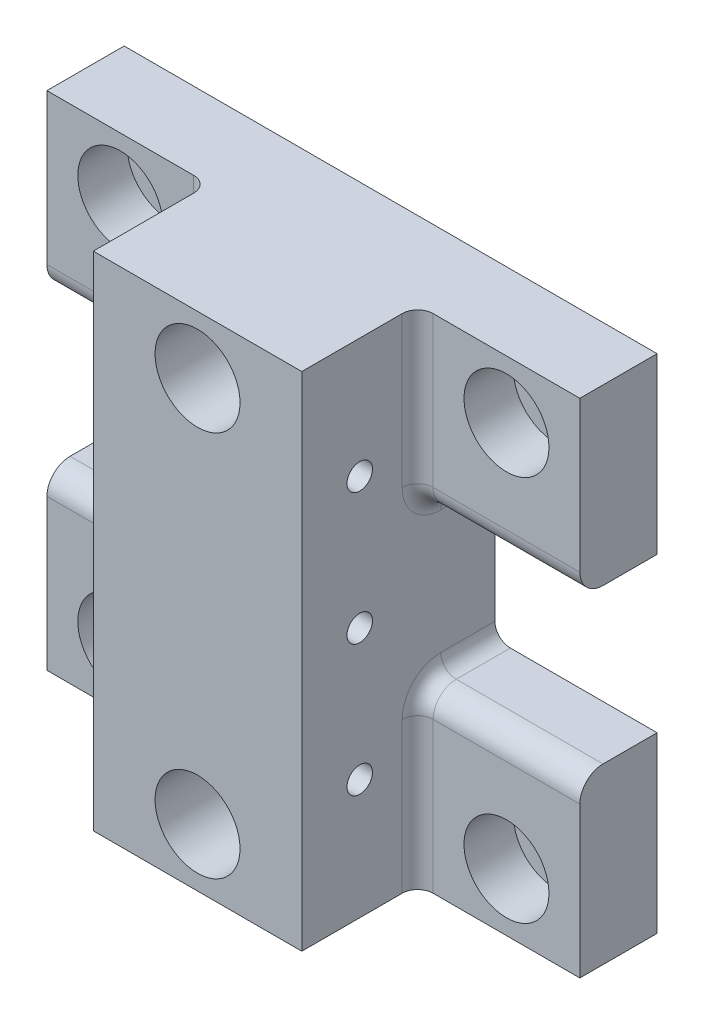
SolidWorks part; units mm, degrees
ref_plane "정면" through (0, 0, 0) normal (0, 0, 1) x (1, 0, 0)
ref_plane "윗면" through (0, 0, 0) normal (0, 1, 0) x (1, 0, 0)
ref_plane "우측면" through (0, 0, 0) normal (1, 0, 0) x (0, 0, -1)
sketch "스케치1" plane through (0, 0, 0) normal (0, 0, 1) x (1, 0, 0)
  line L1 (-34.5, -32.5) -> (34.5, -32.5)
  line L2 (-34.5, -32.5) -> (-34.5, 32.5)
  line L3 (-34.5, 32.5) -> (34.5, 32.5)
  line L4 (34.5, -32.5) -> (34.5, 32.5)
  line L5 (-34.5, -32.5) -> (34.5, 32.5) construction
  line L6 (-34.5, 32.5) -> (34.5, -32.5) construction
  point P0 (0, 0)
  dimension "D1" = 69
  dimension "D2" = 65
extrude "보스-돌출1" add sketch "스케치1" along normal blind 10
sketch "스케치2" plane through (0, 0, 10) normal (0, 0, 1) x (1, 0, 0)
  line L0 (34.5, 32.5) -> (-34.5, 32.5) construction
  line L1 (-13.5, -32.5) -> (13.5, -32.5)
  line L2 (-13.5, -32.5) -> (-13.5, 32.5)
  line L3 (-13.5, 32.5) -> (13.5, 32.5)
  line L4 (13.5, -32.5) -> (13.5, 32.5)
  line L5 (-13.5, -32.5) -> (13.5, 32.5) construction
  line L6 (-13.5, 32.5) -> (13.5, -32.5) construction
  point P0 (0, 0)
  dimension "D1" = 27
extrude "보스-돌출2" add sketch "스케치2" along normal blind 15
sketch "스케치3" plane through (13.5, 0, 0) normal (1, 0, 0) x (0, 0, -1)
  line L0 (0, -32.5) -> (0, 32.5) construction
  line L1 (-10, -10) -> (0, -10)
  line L2 (-10, -10) -> (-10, 10)
  line L3 (-10, 10) -> (0, 10)
  line L4 (0, -10) -> (0, 10)
  line L5 (-10, -10) -> (0, 10) construction
  line L6 (-10, 10) -> (0, -10) construction
  line L7 (-10, -32.5) -> (-10, 32.5) construction
  point P0 (-5, 0)
  dimension "D1" = 20
extrude "컷-돌출1" cut sketch "스케치3" along normal through all
mirror "대칭 복사1" about plane through (0, 0, 0) normal (1, 0, 0) of "컷-돌출1"
fillet "필렛1" radius 3 4 edges at (-24, -10, 10) (-24, 10, 10) (24, -10, 10) (24, 10, 10)
fillet "필렛2" radius 2 12 edges at (13.5, -10, 3.5) (13.5, -10.8787, 9.1213) (-13.5, -10, 3.5) (-13.5, -10.8787, 9.1213) (-13.5, 10, 3.5) (-13.5, 10.8787, 9.1213) (13.5, 10, 3.5) (13.5, 10.8787, 9.1213) (13.5, -22.75, 10) (-13.5, -22.75, 10) (-13.5, 22.75, 10) (13.5, 22.75, 10)
sketch "스케치4" plane through (13.5, 0, 0) normal (1, 0, 0) x (0, 0, -1)
  line L2 (-25, -32.5) -> (-25, 32.5) construction
  circle A0 centre (-17.5, 0) radius 2
  point P0 (-17.5, 0)
  dimension "D2" = 4
  dimension "D1" = 7.5
hole_wizard "M4 탭을 위한 탭 드릴1" positions "스케치7" profile "스케치8" hole size "M4" standard "ISO"
sketch "스케치7" plane through (13.5, 0, 0) normal (1, 0, 0) x (0, 0, -1)
  point P0 (-17.5, 0)
sketch "스케치8" plane through (13.5, 0, 17.5) normal (0, 1, 0) x (0, 0, -1)
  line L0 (0, 0) -> (0, 7.9914)
  line L1 (0, 7.9914) -> (1.65, 7)
  line L2 (1.65, 7) -> (1.65, 0)
  line L5 (1.65, 0) -> (0, 0)
  line L10 (0, 7.9914) -> (-1.65, 7) construction
  line L11 (0, -6.35) -> (0, 107.95) construction
  dimension "구멍 지름" = 3.3
  dimension "구멍 깊이" = 7
  dimension "드릴 각도" = 118
pattern_linear "선형 패턴2" count 2 spacing 17 along (0, -1, 0) count 2 spacing 17 along (0, 1, 0) of "M4 탭을 위한 탭 드릴1"
mirror "대칭 복사3" about plane through (0, 0, 0) normal (1, 0, 0) of "선형 패턴2", "M4 탭을 위한 탭 드릴1"
sketch "스케치9" plane through (0, 0, 10) normal (0, 0, 1) x (1, 0, 0)
  line L1 (-25, -25) -> (25, -25)
  line L2 (-25, -25) -> (-25, 25)
  line L3 (-25, 25) -> (25, 25)
  line L4 (25, -25) -> (25, 25)
  line L5 (-25, -25) -> (25, 25) construction
  line L6 (-25, 25) -> (25, -25) construction
  point P0 (0, 0)
  dimension "D1" = 50
  dimension "D2" = 50
hole_wizard "M6 육각 소켓 머리 캡 나사용 카운터보어1" positions "스케치13" profile "스케치14" counterbore size "M6" standard "ISO"
sketch "스케치13" plane through (0, 0, 10) normal (0, 0, 1) x (1, 0, 0)
  line L0 (-25, 25) -> (25, 25) construction
  line L1 (-25, -25) -> (25, -25) construction
  point P0 (-25, 25)
  point P4 (-25, -25)
  point P7 (25, -25)
  point P10 (25, 25)
  point P13 (0, 25)
  point P17 (0, -25)
sketch "스케치14" plane through (-25, 25, 10) normal (1, 0, 0) x (0, -1, 0)
  line L0 (0, 0) -> (0, 10)
  line L1 (0, 10) -> (3.2, 10)
  line L3 (3.2, 10) -> (3.2, 6.4)
  line L4 (3.2, 6.4) -> (5.5, 6.4)
  line L5 (5.5, 6.4) -> (5.5, 0)
  line L7 (5.5, 0) -> (0, 0)
  line L11 (0, -6.35) -> (0, 107.95) construction
  dimension "관통 구멍 지름" = 6.4
  dimension "관통 구멍 깊이" = 10
  dimension "카운터보어 지름" = 11
  dimension "카운터보어 깊이" = 6.4
sketch "스케치15" plane through (0, 0, 10) normal (0, 0, -1) x (-1, 0, 0)
  circle A0 centre (0, -25) radius 5.5 construction
  circle A1 centre (0, 25) radius 5.5 construction
  circle A2 centre (0, -25) radius 5.5
  circle A3 centre (0, 25) radius 5.5
extrude "컷-돌출3" cut sketch "스케치15" against normal through all
